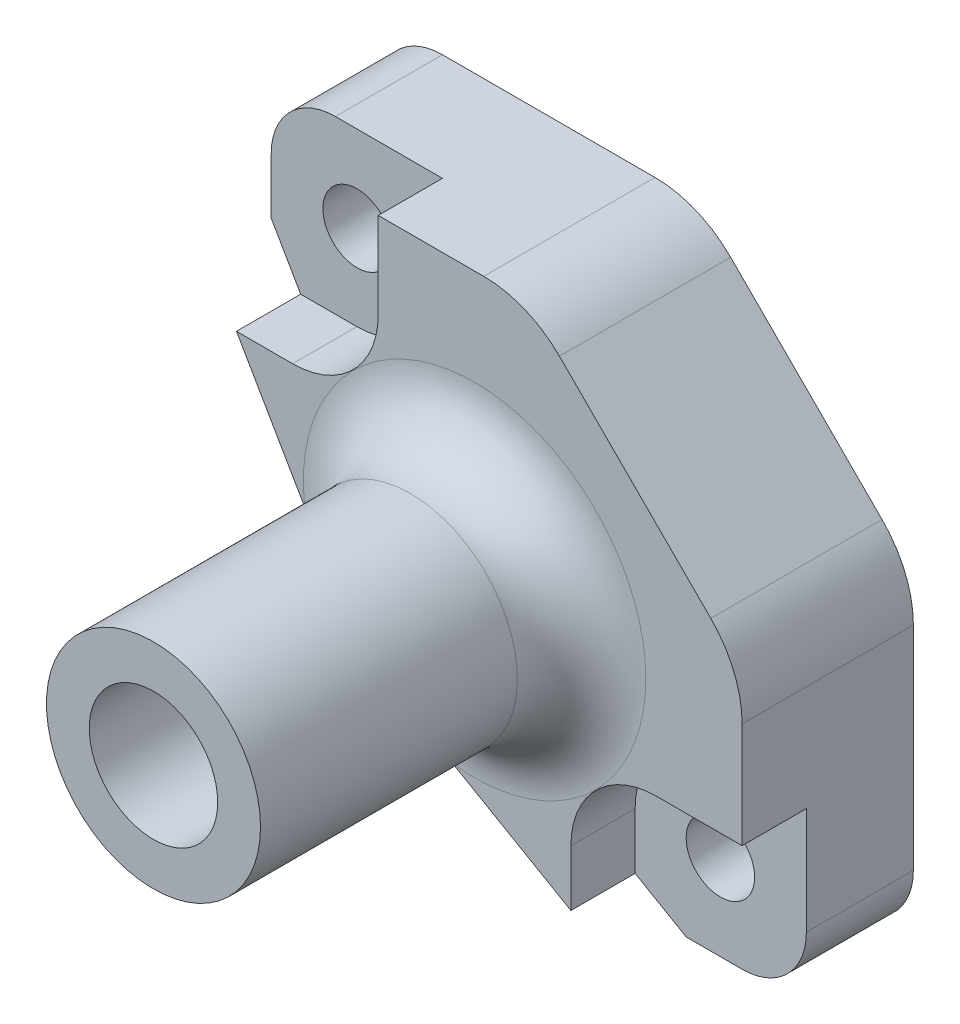
SolidWorks part; units mm, degrees
ref_plane "Piano frontale" through (0, 0, 0) normal (0, 0, 1) x (1, 0, 0)
ref_plane "Piano superiore" through (0, 0, 0) normal (0, 1, 0) x (1, 0, 0)
ref_plane "Piano destro" through (0, 0, 0) normal (1, 0, 0) x (0, 0, -1)
sketch "Schizzo1" plane through (0, 0, 0) normal (0, 0, 1) x (1, 0, 0)
  line L1 (-12.5, 12.5) -> (12.5, 12.5)
  line L2 (-12.5, 12.5) -> (-12.5, -12.5)
  line L3 (-12.5, -12.5) -> (12.5, -12.5)
  line L4 (12.5, 12.5) -> (12.5, -12.5)
  line L5 (-12.5, 12.5) -> (12.5, -12.5) construction
  line L6 (-12.5, -12.5) -> (12.5, 12.5) construction
  point P0 (0, 0)
  dimension "D1" = 25
extrude "Estrusione-Estrusione1" add sketch "Schizzo1" along normal blind 8
sketch "Schizzo8" plane through (0, 0, 8) normal (0, 0, 1) x (1, 0, 0)
  circle A0 centre (0, 0) radius 5
  dimension "D1" = 10
extrude "Estrusione-Estrusione3" add sketch "Schizzo8" along normal blind 15
fillet "Raccordo1" radius 3 1 edges at (5, 0, 8)
sketch "Schizzo9" plane through (0, 0, 0) normal (0, 0, -1) x (-1, 0, 0)
  circle A0 centre (0, 0) radius 1.6
  dimension "D1" = 3.2
extrude "Taglio-Estrusione2" cut sketch "Schizzo9" against normal up to next
sketch "Schizzo10" plane through (0, 0, 0) normal (0, 0, -1) x (-1, 0, 0)
  circle A0 centre (0, 0) radius 3
  dimension "D1" = 6
extrude "Taglio-Estrusione3" cut sketch "Schizzo10" against normal blind 4
sketch "Schizzo11" plane through (0, 0, 23) normal (0, 0, 1) x (1, 0, 0)
  circle A0 centre (0, 0) radius 3
  dimension "D1" = 6
extrude "Taglio-Estrusione4" cut sketch "Schizzo11" against normal blind 16
sketch "Schizzo13" plane through (0, 0, 0) normal (0, 0, -1) x (-1, 0, 0)
  line L0 (-12.5, -12.5) -> (12.5, 12.5) construction
  circle A0 centre (0, 0) radius 12 construction
  circle A1 centre (-8.4853, -8.4853) radius 1.6
  circle A2 centre (8.4853, 8.4853) radius 1.6
  dimension "D1" = 24
  dimension "D2" = 3.2
extrude "Taglio-Estrusione6" cut sketch "Schizzo13" against normal up to next
sketch "Schizzo17" plane through (0, 0, 8) normal (0, 0, 1) x (1, 0, 0)
  line L0 (-12.5, -12.5) -> (12.5, -12.5) construction
  line L1 (4.5, -12.5) -> (4.5, -8.5)
  line L2 (12.5, -4.5) -> (8.5, -4.5)
  line L3 (12.5, -12.5) -> (12.5, 12.5) construction
  line L4 (12.5, -12.5) -> (12.5, -4.5)
  line L5 (4.5, -12.5) -> (12.5, -12.5)
  arc A0 (4.5, -8.5) -> (8.5, -4.5) centre (8.5, -8.5) cw
  dimension "D1" = 4
  dimension "D2" = 8
extrude "Taglio-Estrusione8" cut sketch "Schizzo17" against normal blind 3 and the other way through all
pattern_circular "RipetizioneCircolare1" count 2 over 180 about axis through (0, 0, 0) along (0, 0, 1) of "Taglio-Estrusione8"
sketch "Schizzo18" plane through (0, 0, 8) normal (0, 0, 1) x (1, 0, 0)
  line L5 (2.5, 12.5) -> (12.5, 2.5)
  line L6 (12.5, 12.5) -> (-4.5, 12.5) construction
  line L7 (12.5, -4.5) -> (12.5, 12.5) construction
  line L8 (12.5, 2.5) -> (12.5, 12.5)
  line L9 (12.5, 12.5) -> (2.5, 12.5)
  dimension "D1" = 10
extrude "Taglio-Estrusione9" cut sketch "Schizzo18" against normal up to next
fillet "Raccordo2" radius 5 2 edges at (12.5, 2.5, 4) (2.5, 12.5, 4)
fillet "Raccordo3" radius 3 2 edges at (12.5, -12.5, 2.5) (-12.5, 12.5, 2.5)
sketch "Schizzo19" plane through (0, 0, 8) normal (0, 0, 1) x (1, 0, 0)
  line L0 (4.5, -12.5) -> (9.5, -12.5) construction
  line L2 (-12.5, -12.5) -> (4.5, -12.5) construction
  line L3 (4.5, -12.5) -> (6.8853, -12.5)
  line L4 (-12.5, 4.5) -> (-12.5, -12.5) construction
  line L6 (-12.5, -12.5) -> (4.5, -12.5)
  line L7 (-12.5, 4.5) -> (-12.5, -12.5)
  line L8 (-1.0226, -7.9344) -> (6.8853, -12.5)
  line L9 (6.8853, 10.5197) -> (6.8853, -1.0713) construction
  line L10 (-7.9344, -1.0226) -> (-12.5, 6.8853)
  line L11 (-12.5, 9.5) -> (-12.5, 4.5) construction
  line L12 (-12.5, -12.5) -> (0, 0) construction
  line L13 (-12.5, 6.8853) -> (-12.5, 4.5)
  circle A4 centre (0, 0) radius 8 construction
  circle A5 centre (8.4853, -8.4853) radius 1.6 construction
  arc A6 (-7.9344, -1.0226) -> (-1.0226, -7.9344) centre (8.419, 8.419) ccw
  dimension "D1" = 30
extrude "Taglio-Estrusione10" cut sketch "Schizzo19" against normal up to next and the other way up to next
